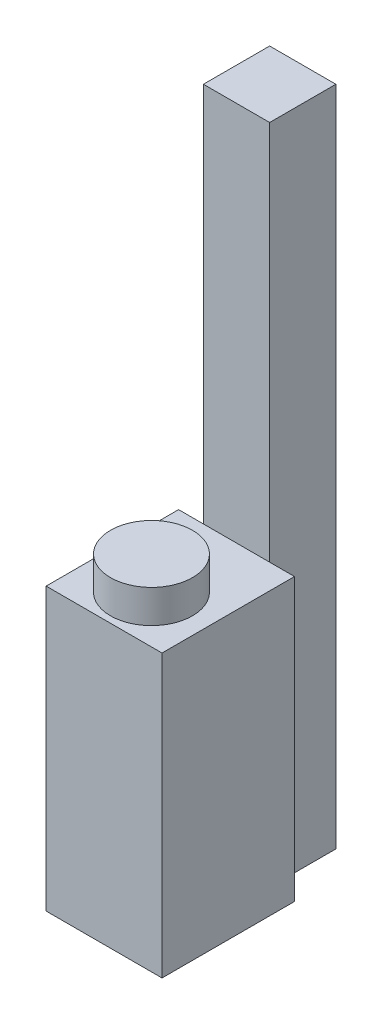
SolidWorks part; units mm, degrees
ref_plane "Ebene vorne" through (0, 0, 0) normal (0, 0, 1) x (1, 0, 0)
ref_plane "Ebene oben" through (0, 0, 0) normal (0, 1, 0) x (1, 0, 0)
ref_plane "Ebene rechts" through (0, 0, 0) normal (1, 0, 0) x (0, 0, -1)
sketch "Skizze1" plane through (0, 0, 0) normal (0, 0, 1) x (1, 0, 0)
  line L1 (-17.5, 42.5) -> (17.5, 42.5)
  line L2 (-17.5, 42.5) -> (-17.5, -42.5)
  line L3 (-17.5, -42.5) -> (17.5, -42.5)
  line L4 (17.5, 42.5) -> (17.5, -42.5)
  line L5 (-17.5, 42.5) -> (17.5, -42.5) construction
  line L6 (-17.5, -42.5) -> (17.5, 42.5) construction
  point P0 (0, 0)
  dimension "D1" = 35
  dimension "D2" = 85
extrude "Aufsatz-Linear austragen1" add sketch "Skizze1" against normal blind 40
sketch "Skizze2" plane through (0, 42.5, 0) normal (0, 1, 0) x (1, 0, 0)
  circle A0 centre (0, 14.3165) radius 12.3844
extrude "Aufsatz-Linear austragen2" add sketch "Skizze2" along normal blind 10
sketch "Skizze3" plane through (0, 0, -40) normal (0, 0, -1) x (-1, 0, 0)
  line L0 (17.5, -42.5) -> (-17.5, -42.5) construction
  line L1 (10, -42.5) -> (-10, -42.5)
  line L2 (10, -42.5) -> (10, 157.5)
  line L3 (10, 157.5) -> (-10, 157.5)
  line L4 (-10, -42.5) -> (-10, 157.5)
  line L5 (0, -42.5) -> (0, 42.5) construction
  line L6 (-17.5, 42.5) -> (17.5, 42.5) construction
  point P10 (0, -42.5)
  dimension "D1" = 20
  dimension "D2" = 200
extrude "Aufsatz-Linear austragen3" add sketch "Skizze3" along normal blind 20
